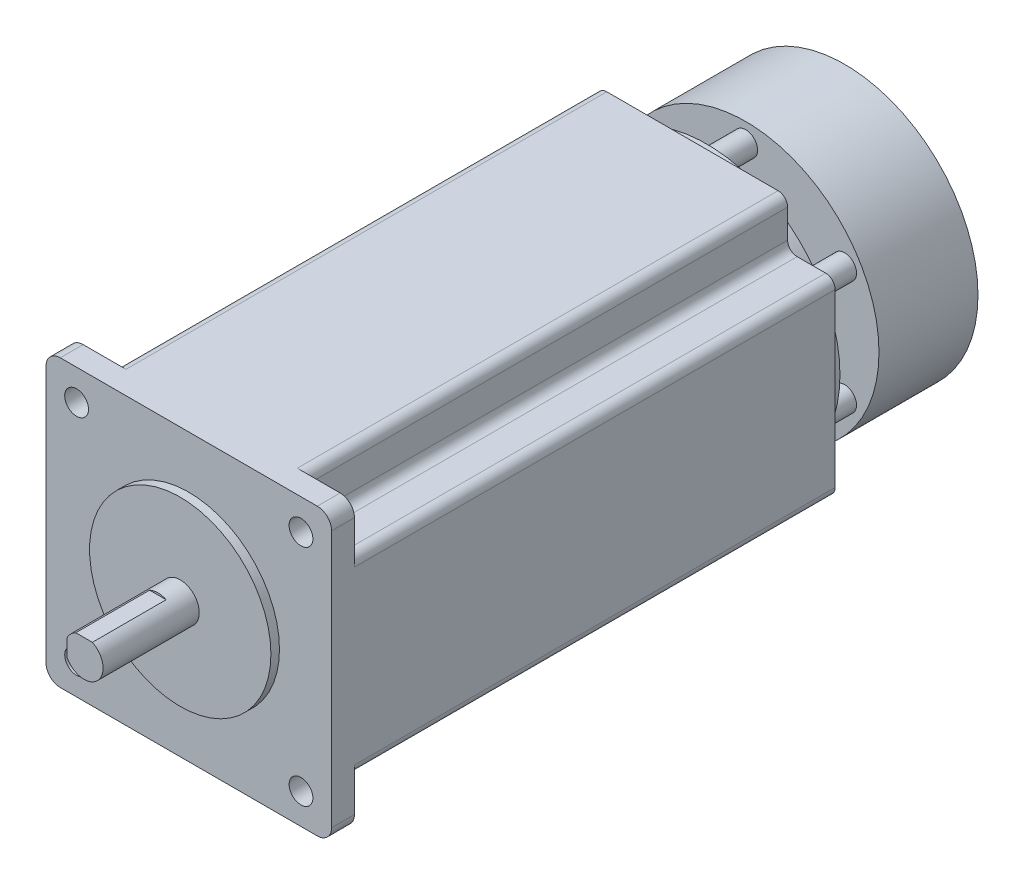
SolidWorks part; units mm, degrees
ref_plane "Front Plane" through (0, 0, 0) normal (0, 0, 1) x (1, 0, 0)
ref_plane "Top Plane" through (0, 0, 0) normal (0, 1, 0) x (1, 0, 0)
ref_plane "Right Plane" through (0, 0, 0) normal (1, 0, 0) x (0, 0, -1)
sketch "Sketch1" plane through (0, 0, 0) normal (0, 0, 1) x (1, 0, 0)
  line L0 (-23.57, 23.57) -> (23.57, 23.57) construction
  line L1 (-27, -30) -> (27, -30)
  line L2 (-30, -27) -> (-30, 27)
  line L3 (-27, 30) -> (27, 30)
  line L4 (30, -27) -> (30, 27)
  line L5 (-30, -30) -> (30, 30) construction
  line L6 (-30, 30) -> (30, -30) construction
  line L7 (0, 23.57) -> (0, 0) construction
  line L8 (0, 0) -> (15.1154, 0) construction
  circle A0 centre (-23.57, 23.57) radius 2.5
  circle A1 centre (23.57, 23.57) radius 2.5
  circle A2 centre (23.57, -23.57) radius 2.5
  circle A3 centre (-23.57, -23.57) radius 2.5
  arc A4 (-30, -27) -> (-27, -30) centre (-27, -27) ccw
  arc A5 (27, -30) -> (30, -27) centre (27, -27) ccw
  arc A6 (30, 27) -> (27, 30) centre (27, 27) ccw
  arc A7 (-27, 30) -> (-30, 27) centre (-27, 27) ccw
  point P0 (0, 0)
  dimension "D5" = 5
  dimension "D6" = 5
  dimension "D7" = 3
  dimension "D1" = 60
  dimension "D2" = 60
  dimension "D3" = 23.57
  dimension "D4" = 47.14
extrude "Boss-Extrude1" add sketch "Sketch1" against normal blind 4.8
sketch "Sketch3" plane through (0, 0, -4.8) normal (0, 0, -1) x (-1, 0, 0)
  line L0 (0, 0) -> (0, 30) construction
  line L1 (-27, 30) -> (27, 30) construction
  line L2 (0, 0) -> (-30, 0) construction
  line L3 (-30, -27) -> (-30, 27) construction
  line L4 (18, 30) -> (-18, 30)
  line L5 (-20, 28) -> (-20, 22)
  line L6 (-22, 20) -> (-28, 20)
  line L7 (-30, 18) -> (-30, -18)
  line L8 (30, 18) -> (30, -18)
  line L9 (22, 20) -> (28, 20)
  line L10 (20, 28) -> (20, 22)
  line L11 (20, -28) -> (20, -22)
  line L12 (22, -20) -> (28, -20)
  line L13 (-22, -20) -> (-28, -20)
  line L14 (-20, -28) -> (-20, -22)
  line L15 (18, -30) -> (-18, -30)
  arc A0 (-18, 30) -> (-20, 28) centre (-18, 28) ccw
  arc A1 (-20, 22) -> (-22, 20) centre (-22, 22) cw
  arc A2 (-28, 20) -> (-30, 18) centre (-28, 18) ccw
  arc A3 (28, 20) -> (30, 18) centre (28, 18) cw
  arc A4 (20, 22) -> (22, 20) centre (22, 22) ccw
  arc A5 (18, 30) -> (20, 28) centre (18, 28) cw
  arc A6 (18, -30) -> (20, -28) centre (18, -28) ccw
  arc A7 (20, -22) -> (22, -20) centre (22, -22) cw
  arc A8 (28, -20) -> (30, -18) centre (28, -18) ccw
  arc A9 (-28, -20) -> (-30, -18) centre (-28, -18) cw
  arc A10 (-20, -22) -> (-22, -20) centre (-22, -22) ccw
  arc A11 (-18, -30) -> (-20, -28) centre (-18, -28) cw
  point P13 (-20, 30)
  point P18 (-30, 20)
  point P30 (30, 0)
  point P47 (-30, -20)
  point P48 (-20, -30)
  dimension "D3" = 2
  dimension "D1" = 10
  dimension "D2" = 10
extrude "Boss-Extrude2" add sketch "Sketch3" along normal blind 101
sketch "Sketch4" plane through (0, 0, 0) normal (0, 0, 1) x (1, 0, 0)
  circle A0 centre (0, 0) radius 19.05
  dimension "D1" = 38.1
extrude "Boss-Extrude3" add sketch "Sketch4" along normal blind 1.8
sketch "Sketch5" plane through (0, 0, 1.8) normal (0, 0, 1) x (1, 0, 0)
  circle A0 centre (0, 0) radius 4
  dimension "D1" = 8
extrude "Boss-Extrude4" add sketch "Sketch5" along normal blind 20.2
sketch "Sketch7" plane through (0, 0, 22) normal (0, 0, 1) x (1, 0, 0)
  line L0 (-1.7436, 3.6) -> (1.7436, 3.6)
  line L1 (0, 4) -> (0, -4) construction
  line L2 (-4, 0) -> (4, 0) construction
  line L3 (-3.6, 1.7436) -> (-3.6, -1.7436)
  arc A0 (1.7436, 3.6) -> (-1.7436, 3.6) centre (0, 0) ccw
  circle A1 centre (0, 0) radius 4
  arc A2 (-3.6, 1.7436) -> (-3.6, -1.7436) centre (0, 0) ccw
  point P4 (0, 0)
  point P10 (0, 0)
  point P14 (0, 0)
  dimension "D2" = 7.6
  dimension "D3" = 7.6
  dimension "D1" = 0
extrude "Cut-Extrude1" cut sketch "Sketch7" against normal blind 15.5
sketch "Sketch8" plane through (0, 0, -105.8) normal (0, 0, -1) x (-1, 0, 0)
  circle A0 centre (0, 0) radius 28
  dimension "D1" = 56
extrude "Boss-Extrude5" add sketch "Sketch8" along normal blind 3
sketch "Sketch9" plane through (0, 0, -108.8) normal (0, 0, -1) x (-1, 0, 0)
  line L0 (0, 0) -> (0, 24) construction
  circle A0 centre (0, 0) radius 24 construction
  circle A1 centre (0, 24) radius 2.5
  circle A2 centre (20.7846, 12) radius 2.5
  circle A3 centre (20.7846, -12) radius 2.5
  circle A4 centre (0, -24) radius 2.5
  circle A5 centre (-20.7846, -12) radius 2.5
  circle A6 centre (-20.7846, 12) radius 2.5
  point P17 (0, 0)
  dimension "D1" = 48
  dimension "D2" = 5
  dimension "D3" = 6
extrude "Boss-Extrude6" add sketch "Sketch9" along normal blind 8.2
sketch "Sketch10" plane through (0, 0, -117) normal (0, 0, -1) x (-1, 0, 0)
  circle A0 centre (0, 0) radius 28 construction
  circle A1 centre (0, 0) radius 28
extrude "Boss-Extrude7" add sketch "Sketch10" along normal blind 20.8
sketch "Sketch11" plane through (0, 0, -105.8) normal (0, 0, -1) x (-1, 0, 0)
  line L0 (-18, -30) -> (18, -30) construction
  line L1 (-10.5, -30) -> (10.5, -30)
  line L2 (-10.5, -30) -> (-10.5, -39)
  line L3 (-10.5, -39) -> (10.5, -39)
  line L4 (10.5, -30) -> (10.5, -39)
  line L5 (0, -39) -> (0, 0) construction
  dimension "D1" = 21
  dimension "D2" = 9
extrude "Boss-Extrude8" add sketch "Sketch11" against normal blind 17
chamfer "Chamfer1" distance 1 angle 45 2 edges at (-10.5, -39, -97.3) (10.5, -39, -97.3)
sketch "Sketch12" plane through (0, 0, -137.8) normal (0, 0, -1) x (-1, 0, 0)
  circle A0 centre (0, 0) radius 4
  dimension "D1" = 8
extrude "Boss-Extrude9" add sketch "Sketch12" against normal up to surface (29 mm away) up to face at (18.2846, 12, -108.8)
equation "\"D6@Sketch1\"=\"D5@Sketch1\""
